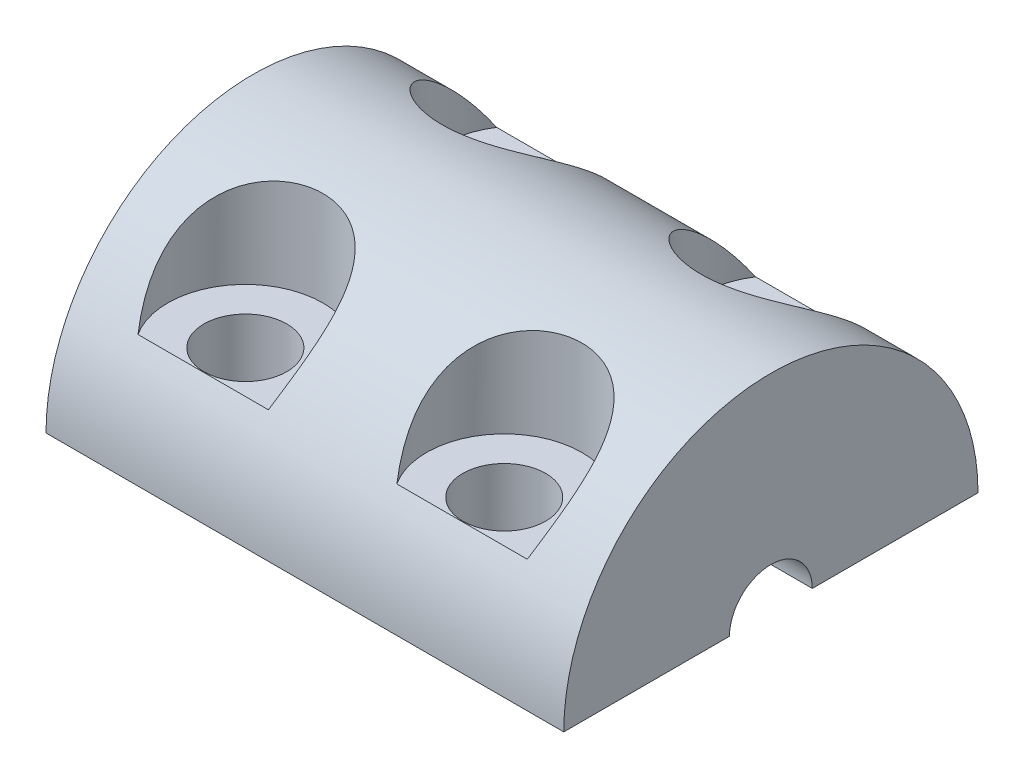
SolidWorks part; units mm, degrees
ref_plane "Front Plane" through (0, 0, 0) normal (0, 0, 1) x (1, 0, 0)
ref_plane "Top Plane" through (0, 0, 0) normal (0, 1, 0) x (1, 0, 0)
ref_plane "Right Plane" through (0, 0, 0) normal (1, 0, 0) x (0, 0, -1)
sketch "Sketch2" plane through (0, 0, 0) normal (1, 0, 0) x (0, 0, -1)
  line L0 (-8, 0) -> (-1.6, 0)
  line L1 (1.6, 0) -> (8, 0)
  arc A0 (-8, 0) -> (8, 0) centre (0, 0) cw
  arc A1 (-1.6, 0) -> (1.6, 0) centre (0, 0) cw
extrude "Boss-Extrude1" add sketch "Sketch2" along normal blind 10
sketch "Sketch3" plane through (0, 0, 0) normal (-1, 0, 0) x (0, 0, 1)
  line L2 (-8, 0) -> (-1.6, 0)
  line L3 (1.6, 0) -> (8, 0)
  line L4 (-8, 0) -> (-2.6, 0)
  line L5 (2.6, 0) -> (8, 0)
  arc A0 (-2.6, 0) -> (2.6, 0) centre (0, 0) cw
  arc A2 (8, 0) -> (-8, 0) centre (0, 0) ccw
  arc A3 (1.6, 0) -> (-1.6, 0) centre (0, 0) ccw
  arc A4 (8, 0) -> (-8, 0) centre (0, 0) ccw
  dimension "D1" = 0
extrude "Boss-Extrude2" add sketch "Sketch3" along normal blind 10
sketch "Sketch4" plane through (0, 0, 0) normal (0, -1, 0) x (1, 0, 0)
  line L0 (-10, 5.3) -> (10, 5.3) construction
  line L1 (-10, 2.6) -> (-10, 8) construction
  line L2 (10, 8) -> (10, 1.6) construction
  line L3 (10, 5.3) -> (10, 0) construction
  line L4 (10, 0) -> (-9.596, 0) construction
  circle A0 centre (-5, 5.3) radius 1.6
  circle A1 centre (5, 5.3) radius 1.6
  circle A2 centre (-5, -5.3) radius 1.6
  circle A3 centre (5, -5.3) radius 1.6
  dimension "D1" = 5
  dimension "D2" = 5
extrude "Cut-Extrude1" cut sketch "Sketch4" against normal blind 10
ref_plane "Plane1" through (0, 4, 0) normal (0, -1, 0) x (-1, 0, 0)
sketch "Sketch5" plane through (0, 4, 0) normal (0, -1, 0) x (-1, 0, 0)
  line L0 (-10.9047, 0) -> (0, 0) construction
  circle A0 centre (-5, 5.3) radius 1.6 construction
  circle A1 centre (-5, 5.3) radius 1.6
  circle A2 centre (5, 5.3) radius 1.6 construction
  circle A3 centre (5, 5.3) radius 1.6
  circle A4 centre (-5, 5.3) radius 3
  circle A5 centre (5, 5.3) radius 3
  circle A6 centre (5, -5.3) radius 3
  circle A7 centre (-5, -5.3) radius 3
extrude "Cut-Extrude2" cut sketch "Sketch5" against normal blind 10
